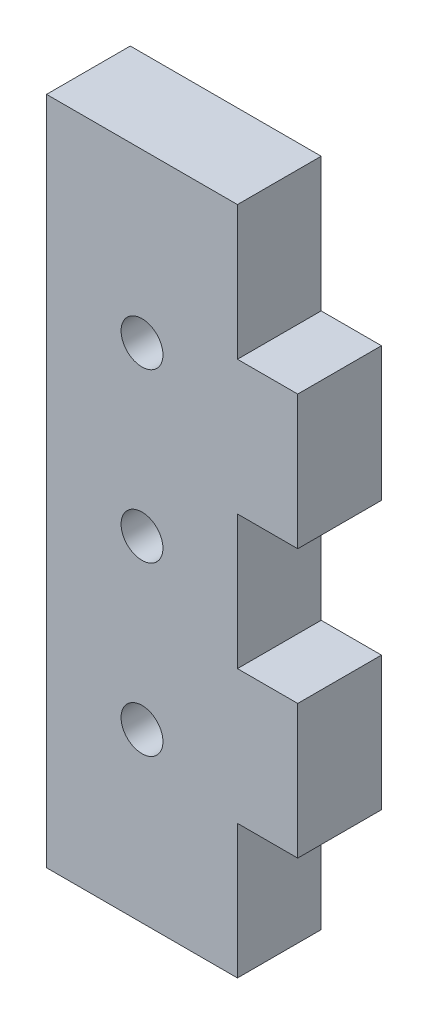
SolidWorks part; units mm, degrees
ref_plane "Front Plane" through (0, 0, 0) normal (0, 0, 1) x (1, 0, 0)
ref_plane "Top Plane" through (0, 0, 0) normal (0, 1, 0) x (1, 0, 0)
ref_plane "Right Plane" through (0, 0, 0) normal (1, 0, 0) x (0, 0, -1)
sketch "Sketch1" plane through (0, 0, 0) normal (0, 0, 1) x (1, 0, 0)
  line L1 (0, 0) -> (19.05, 0)
  line L2 (0, 0) -> (0, 50.8)
  line L3 (0, 50.8) -> (19.05, 50.8)
  line L4 (19.05, 0) -> (19.05, 50.8)
  dimension "D1" = 19.05
  dimension "D2" = 50.8
extrude "Boss-Extrude1" add sketch "Sketch1" along normal blind 6.35
sketch "Sketch2" plane through (0, 0, 6.35) normal (0, 0, 1) x (1, 0, 0)
  line L0 (19.05, 0) -> (19.05, 50.8) construction
  line L1 (19.05, 50.8) -> (14.478, 50.8)
  line L2 (19.05, 50.8) -> (19.05, 40.64)
  line L3 (19.05, 40.64) -> (14.478, 40.64)
  line L4 (14.478, 50.8) -> (14.478, 40.64)
  line L5 (19.05, 30.48) -> (14.478, 30.48)
  line L6 (19.05, 30.48) -> (19.05, 20.32)
  line L7 (19.05, 20.32) -> (14.478, 20.32)
  line L8 (14.478, 30.48) -> (14.478, 20.32)
  line L9 (0, 0) -> (19.05, 0) construction
  line L10 (19.05, 10.16) -> (14.478, 10.16)
  line L11 (19.05, 10.16) -> (19.05, 0)
  line L12 (19.05, 0) -> (14.478, 0)
  line L13 (14.478, 10.16) -> (14.478, 0)
  line L14 (14.478, 40.64) -> (14.478, 30.48) construction
  line L15 (14.478, 20.32) -> (14.478, 10.16) construction
  dimension "D1" = 4.572
extrude "Cut-Extrude1" cut sketch "Sketch2" against normal through all
sketch "Sketch3" plane through (0, 0, 6.35) normal (0, 0, 1) x (1, 0, 0)
  line L0 (7.239, 12.7) -> (7.239, 25.4) construction
  line L1 (14.478, 50.8) -> (0, 50.8) construction
  line L2 (0, 0) -> (14.478, 0) construction
  line L3 (7.239, 0) -> (7.239, 12.7) construction
  line L4 (7.239, 25.4) -> (7.239, 38.1) construction
  line L5 (7.239, 38.1) -> (7.239, 50.8) construction
  circle A0 centre (7.239, 38.1) radius 1.5875
  circle A1 centre (7.239, 25.4) radius 1.5875
  circle A2 centre (7.239, 12.7) radius 1.5875
  dimension "D1" = 3.175
  dimension "D2" = 3.175
  dimension "D3" = 3.175
extrude "Cut-Extrude2" cut sketch "Sketch3" against normal through all
